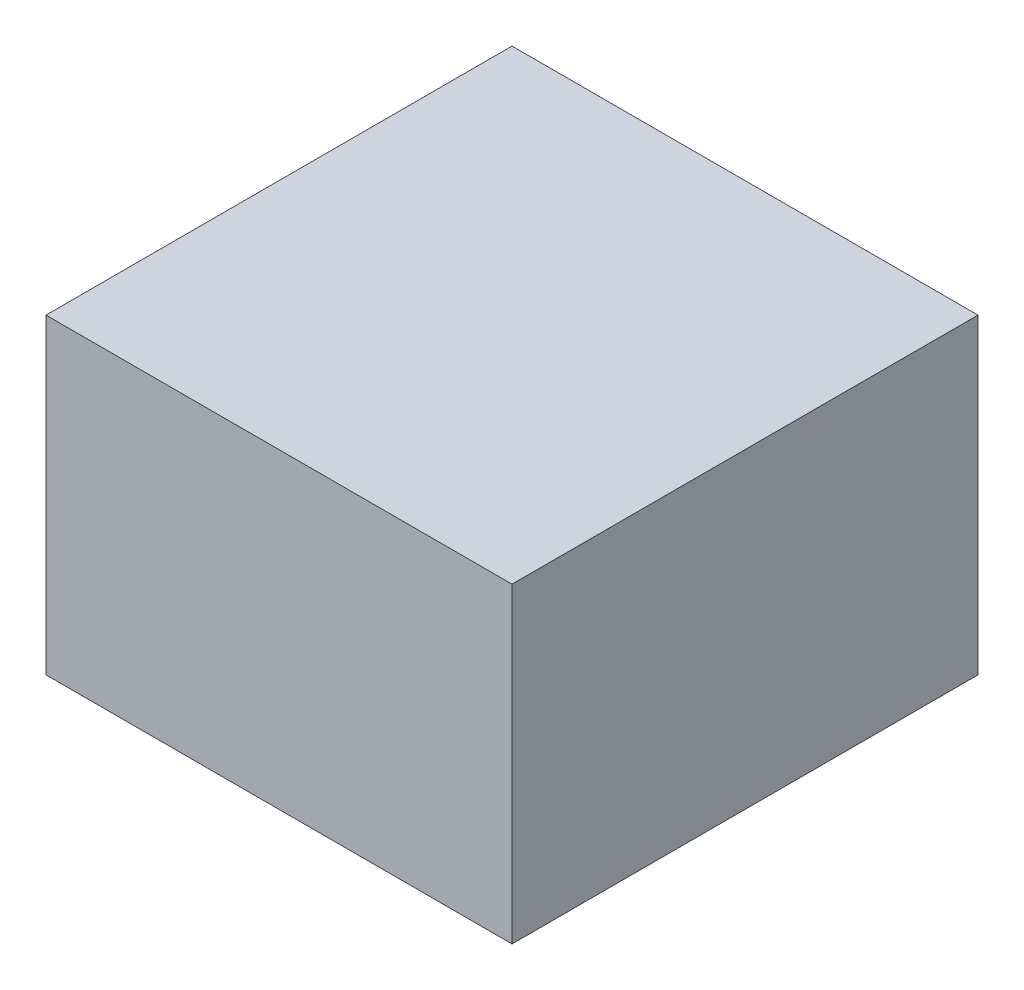
SolidWorks part; units mm, degrees
ref_plane "Front Plane" through (0, 0, 0) normal (0, 0, 1) x (1, 0, 0)
ref_plane "Top Plane" through (0, 0, 0) normal (0, 1, 0) x (1, 0, 0)
ref_plane "Right Plane" through (0, 0, 0) normal (1, 0, 0) x (0, 0, -1)
sketch "Sketch1" plane through (0, 0, 0) normal (0, 1, 0) x (1, 0, 0)
  line L1 (-38.5, 38.5) -> (28.5, 38.5)
  line L2 (-38.5, 38.5) -> (-38.5, -28.5)
  line L3 (-38.5, -28.5) -> (28.5, -28.5)
  line L4 (28.5, 38.5) -> (28.5, -28.5)
  dimension "D1" = 67
  dimension "D2" = 67
  dimension "D3" = 38.5
  dimension "D4" = 38.5
extrude "Boss-Extrude1" add sketch "Sketch1" along normal mid plane 44.8
